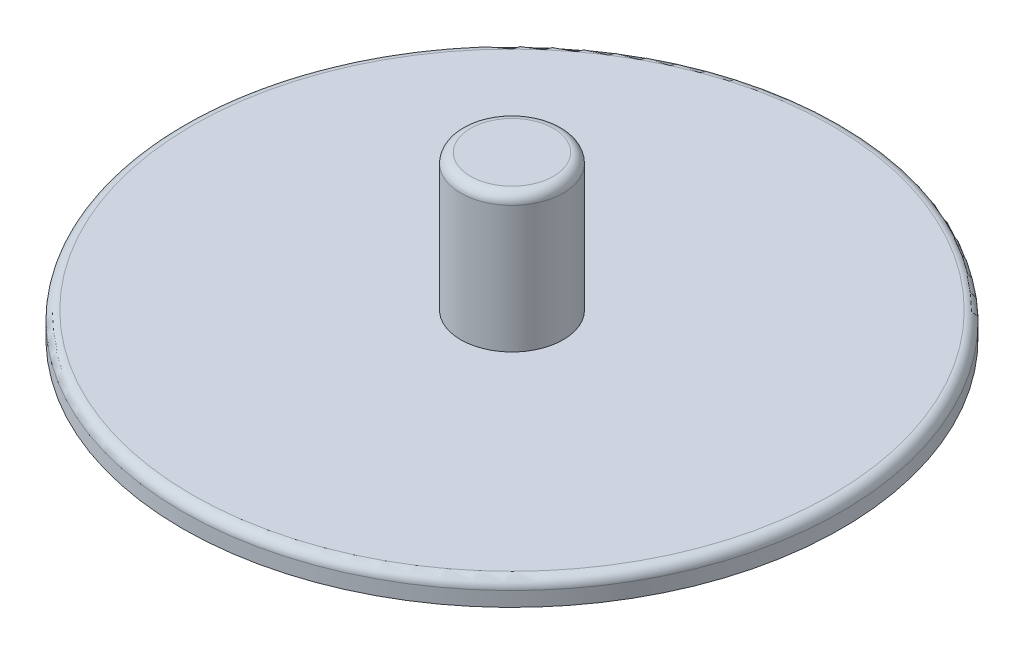
SolidWorks part; units mm, degrees
ref_plane "Front Plane" through (0, 0, 0) normal (0, 0, 1) x (1, 0, 0)
ref_plane "Top Plane" through (0, 0, 0) normal (0, 1, 0) x (1, 0, 0)
ref_plane "Right Plane" through (0, 0, 0) normal (1, 0, 0) x (0, 0, -1)
sketch "Sketch1" plane through (0, 0, 0) normal (0, 1, 0) x (1, 0, 0)
  circle A0 centre (0, 0) radius 85.725
  dimension "D2" = 171.45
extrude "Boss-Extrude1" add sketch "Sketch1" along normal blind 6.35
sketch "Sketch2" plane through (0, 6.35, 0) normal (0, 1, 0) x (1, 0, 0)
  circle A0 centre (0, 0) radius 13.335
  dimension "D1" = 26.67
extrude "Boss-Extrude2" add sketch "Sketch2" along normal blind 35.56
fillet "Fillet1" radius 2.54 1 edges at (0, 41.91, 13.335)
fillet "Fillet2" radius 2.54 1 edges at (0, 6.35, 85.725)
